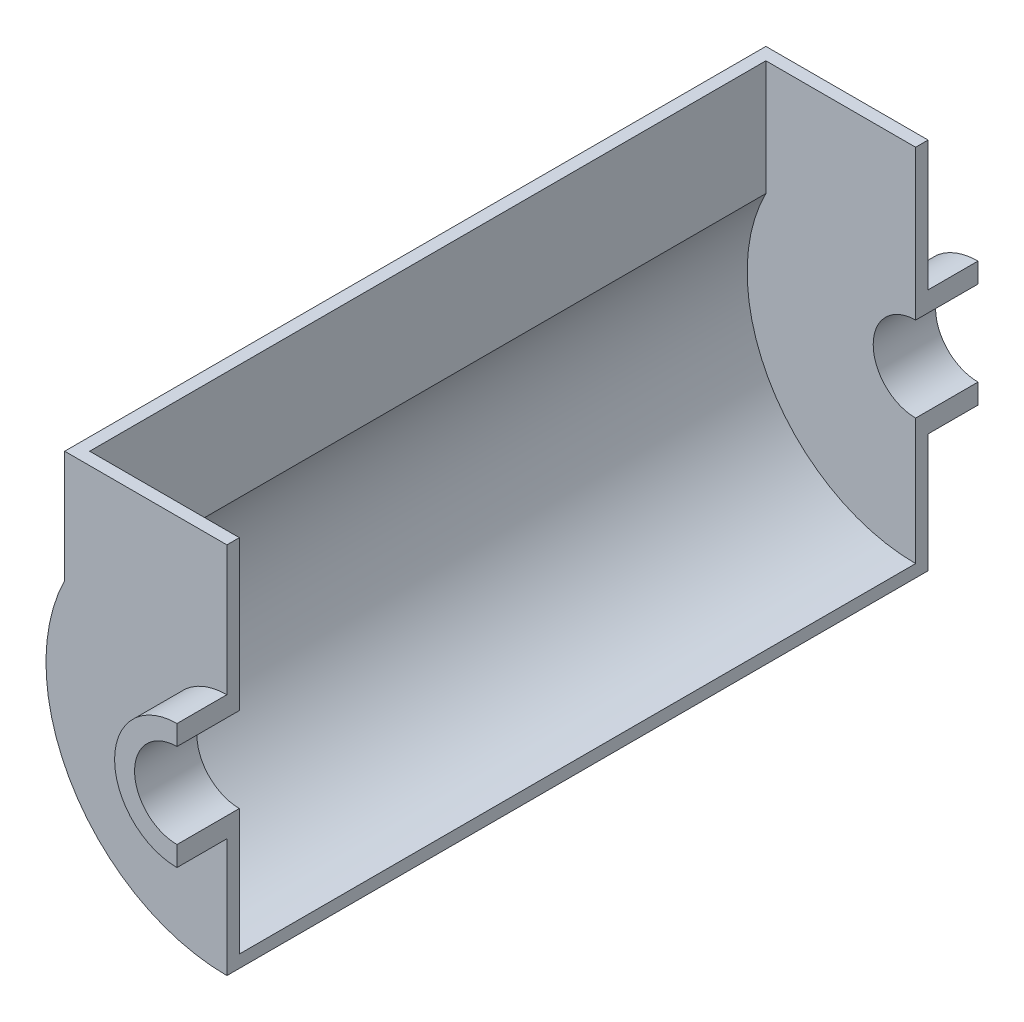
SolidWorks part; units mm, degrees
ref_plane "Front Plane" through (0, 0, 0) normal (0, 0, 1) x (1, 0, 0)
ref_plane "Top Plane" through (0, 0, 0) normal (0, 1, 0) x (1, 0, 0)
ref_plane "Right Plane" through (0, 0, 0) normal (1, 0, 0) x (0, 0, -1)
sketch "Sketch1" plane through (0, 0, 0) normal (0, 0, 1) x (1, 0, 0)
  line L0 (0, 25) -> (0, 17)
  line L1 (0, -17) -> (0, -25)
  arc A0 (0, 17) -> (0, -17) centre (0, 0) ccw
  arc A1 (0, 25) -> (0, -25) centre (0, 0) ccw
  dimension "D1" = 50
  dimension "D2" = 34
extrude "Boss-Extrude1" add sketch "Sketch1" along normal blind 20 and the other way blind 5
sketch "Sketch2" plane through (0, 0, 0) normal (0, 0, 1) x (1, 0, 0)
  line L0 (0, 25) -> (0, 77)
  line L1 (0, 77) -> (-65, 77)
  line L2 (-65, 77) -> (-65, 32.1131)
  line L3 (0, -25) -> (0, -72.5)
  arc A0 (0, 25) -> (0, -25) centre (0, 0) ccw construction
  arc A1 (0, 25) -> (0, -25) centre (0, 0) ccw
  arc A2 (0, -72.5) -> (-65, 32.1131) centre (0, 0) cw
  dimension "D3" = 72.5
  dimension "D1" = 52
  dimension "D2" = 65
extrude "Boss-Extrude2" add sketch "Sketch2" against normal blind 5
ref_plane "Plane1" through (0, 0, -140.5) normal (0, 0, 1) x (1, 0, 0)
mirror "Mirror1" about plane through (0, 0, -140.5) normal (0, 0, 1) of bodies 102
sketch "Sketch3" plane through (0, 0, -5) normal (0, 0, -1) x (-1, 0, 0)
  line L0 (65, 77) -> (65, 32.1131) construction
  line L1 (65, 77) -> (65, 32.1131)
  line L2 (60, 77) -> (60, 30.9233)
  line L3 (65, 77) -> (60, 77)
  line L4 (0, -72.5) -> (0, -67.5)
  arc A0 (0, -72.5) -> (65, 32.1131) centre (0, 0) ccw construction
  arc A1 (0, -72.5) -> (65, 32.1131) centre (0, 0) ccw
  arc A2 (0, -67.5) -> (60, 30.9233) centre (0, 0) ccw
  dimension "D1" = 5
extrude "Boss-Extrude3" add sketch "Sketch3" along normal up to surface (271 mm away)
